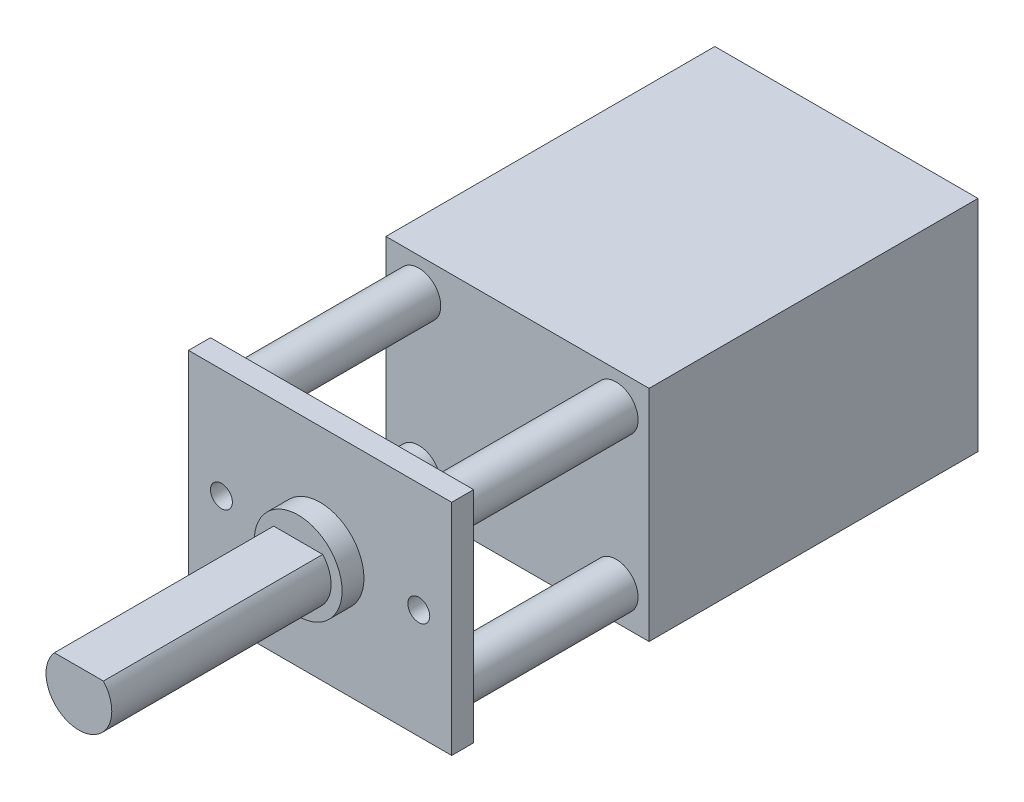
SolidWorks part; units mm, degrees
ref_plane "前视基准面" through (0, 0, 0) normal (0, 0, 1) x (1, 0, 0)
ref_plane "上视基准面" through (0, 0, 0) normal (0, 1, 0) x (1, 0, 0)
ref_plane "右视基准面" through (0, 0, 0) normal (1, 0, 0) x (0, 0, -1)
sketch "草图1" plane through (0, 0, 0) normal (0, 0, 1) x (1, 0, 0)
  line L1 (-6, 5) -> (6, 5)
  line L2 (-6, 5) -> (-6, -5)
  line L3 (-6, -5) -> (6, -5)
  line L4 (6, 5) -> (6, -5)
  line L5 (-6, 5) -> (6, -5) construction
  line L6 (-6, -5) -> (6, 5) construction
  point P0 (0, 0)
  dimension "D1" = 12
  dimension "D2" = 10
extrude "凸台-拉伸1" add sketch "草图1" along normal blind 1
sketch "草图2" plane through (0, 0, 0) normal (0, 0, -1) x (-1, 0, 0)
  line L0 (0, 0) -> (0, -6.6719) construction
  line L1 (0, 0) -> (6.7195, 0) construction
  circle A0 centre (-4.5, 3.5) radius 1
  circle A1 centre (4.5, 3.5) radius 1
  circle A2 centre (4.5, -3.5) radius 1
  circle A3 centre (-4.5, -3.5) radius 1
  dimension "D1" = 2
  dimension "D2" = 4.5
  dimension "D3" = 3.5
extrude "凸台-拉伸2" add sketch "草图2" along normal blind 8
sketch "草图3" plane through (0, 0, 1) normal (0, 0, 1) x (1, 0, 0)
  circle A0 centre (0, 0) radius 2
  dimension "D1" = 4
extrude "凸台-拉伸3" add sketch "草图3" along normal blind 1
sketch "草图4" plane through (0, 0, 2) normal (0, 0, 1) x (1, 0, 0)
  line L0 (-1.118, 1) -> (1.118, 1)
  arc A0 (-1.118, 1) -> (1.118, 1) centre (0, 0) ccw
  dimension "D1" = 3
  dimension "D2" = 1
extrude "凸台-拉伸4" add sketch "草图4" along normal blind 10
sketch "草图5" plane through (0, 0, -8) normal (0, 0, -1) x (-1, 0, 0)
  line L1 (-6, 5) -> (6, 5)
  line L2 (-6, 5) -> (-6, -5)
  line L3 (-6, -5) -> (6, -5)
  line L4 (6, 5) -> (6, -5)
extrude "凸台-拉伸5" add sketch "草图5" along normal blind 15
sketch "草图6" plane through (0, 0, 0) normal (0, 0, -1) x (-1, 0, 0)
  line L0 (0, 0) -> (0, 8.3473) construction
  circle A0 centre (-4.5, 0) radius 0.5
  circle A1 centre (4.5, 0) radius 0.5
  dimension "D1" = 1
  dimension "D2" = 4.5
extrude "切除-拉伸1" cut sketch "草图6" against normal up to next
